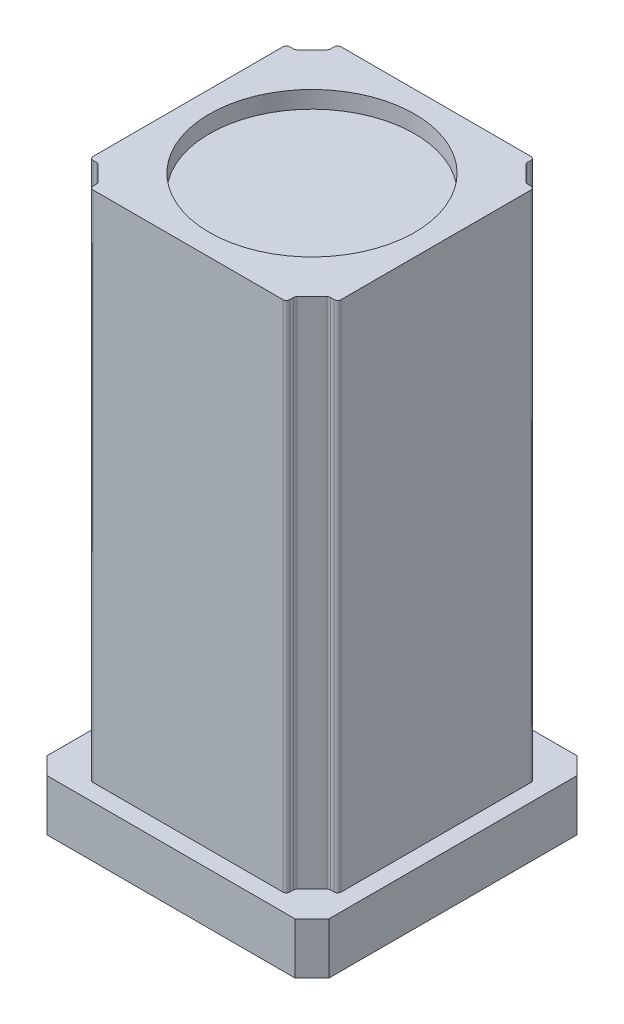
SolidWorks part; units mm, degrees
ref_plane "Front Plane" through (0, 0, 0) normal (0, 0, 1) x (1, 0, 0)
ref_plane "Top Plane" through (0, 0, 0) normal (0, 1, 0) x (1, 0, 0)
ref_plane "Right Plane" through (0, 0, 0) normal (1, 0, 0) x (0, 0, -1)
sketch "Sketch1" plane through (0, 0, 0) normal (0, 1, 0) x (1, 0, 0)
  line L0 (-82.5, 72.5) -> (-72.5, 82.5)
  line L1 (-72.5, -82.5) -> (72.5, -82.5)
  line L2 (-82.5, -72.5) -> (-82.5, 72.5)
  line L3 (-72.5, 82.5) -> (72.5, 82.5)
  line L4 (82.5, -72.5) -> (82.5, 72.5)
  line L5 (-82.5, -82.5) -> (82.5, 82.5) construction
  line L6 (-82.5, 82.5) -> (82.5, -82.5) construction
  line L7 (72.5, 82.5) -> (82.5, 72.5)
  line L8 (72.5, -82.5) -> (82.5, -72.5)
  line L9 (-82.5, -72.5) -> (-72.5, -82.5)
  point P0 (0, 0)
  dimension "D1" = 165
  dimension "D2" = 165
  dimension "D3" = 10
  dimension "D4" = 45
  dimension "D5" = 10
  dimension "D6" = 45
  dimension "D7" = 10
  dimension "D8" = 45
  dimension "D9" = 10
  dimension "D10" = 45
extrude "Boss-Extrude1" add sketch "Sketch1" along normal blind 30
sketch "Sketch2" plane through (0, 30, 0) normal (0, 1, 0) x (1, 0, 0)
  line L0 (-72.5, 82.5) -> (-82.5, 72.5) construction
  line L1 (-62.5, 62.5) -> (-57.5, 57.5) construction
  line L2 (72.5, 57.5) -> (67.5, 57.5)
  line L3 (-72.5, 57.5) -> (-67.5, 57.5)
  line L4 (-57.5, 72.5) -> (-57.5, 67.5)
  line L5 (67.5, 57.5) -> (57.5, 67.5)
  line L6 (57.5, 72.5) -> (57.5, 67.5)
  line L7 (-67.5, 57.5) -> (-57.5, 67.5)
  line L8 (0, 63.027) -> (0, -43.1238) construction
  line L9 (0, 0) -> (121.2625, 0) construction
  line L10 (-57.5, -72.5) -> (-57.5, -67.5)
  line L11 (-67.5, -57.5) -> (-57.5, -67.5)
  line L12 (-72.5, -57.5) -> (-67.5, -57.5)
  line L13 (57.5, -72.5) -> (57.5, -67.5)
  line L14 (72.5, -57.5) -> (67.5, -57.5)
  line L15 (67.5, -57.5) -> (57.5, -67.5)
  line L44 (72.5, 68.3579) -> (68.3579, 72.5)
  line L45 (72.5, -68.3579) -> (72.5, 68.3579)
  line L46 (68.3579, -72.5) -> (72.5, -68.3579)
  line L47 (-68.3579, -72.5) -> (68.3579, -72.5)
  line L48 (-72.5, -68.3579) -> (-68.3579, -72.5)
  line L49 (-72.5, 68.3579) -> (-72.5, -68.3579)
  line L50 (-68.3579, 72.5) -> (-72.5, 68.3579)
  line L51 (68.3579, 72.5) -> (-68.3579, 72.5)
  line L53 (72.5, -57.5) -> (72.5, 57.5)
  line L55 (-57.5, -72.5) -> (57.5, -72.5)
  line L57 (-72.5, 57.5) -> (-72.5, -57.5)
  line L59 (57.5, 72.5) -> (-57.5, 72.5)
  point P0 (-77.5, 77.5)
  dimension "D4" = 10
  dimension "D5" = 45
  dimension "D1" = 10
extrude "Boss-Extrude2" add sketch "Sketch2" along normal blind 300
sketch "Sketch3" plane through (0, 330, 0) normal (0, 1, 0) x (1, 0, 0)
  circle A0 centre (0, 0) radius 60
  dimension "D1" = 120
extrude "Cut-Extrude1" cut sketch "Sketch3" against normal blind 10
fillet "Fillet1" radius 2 16 edges at (72.5, 180, 57.5) (67.5, 180, 57.5) (57.5, 180, 67.5) (57.5, 180, 72.5) (-57.5, 180, 72.5) (-57.5, 180, 67.5) (-67.5, 180, 57.5) (-72.5, 180, 57.5) (-67.5, 180, -57.5) (-57.5, 180, -67.5) (-57.5, 180, -72.5) (57.5, 180, -72.5) (57.5, 180, -67.5) (67.5, 180, -57.5) (72.5, 180, -57.5) (-72.5, 180, -57.5)
